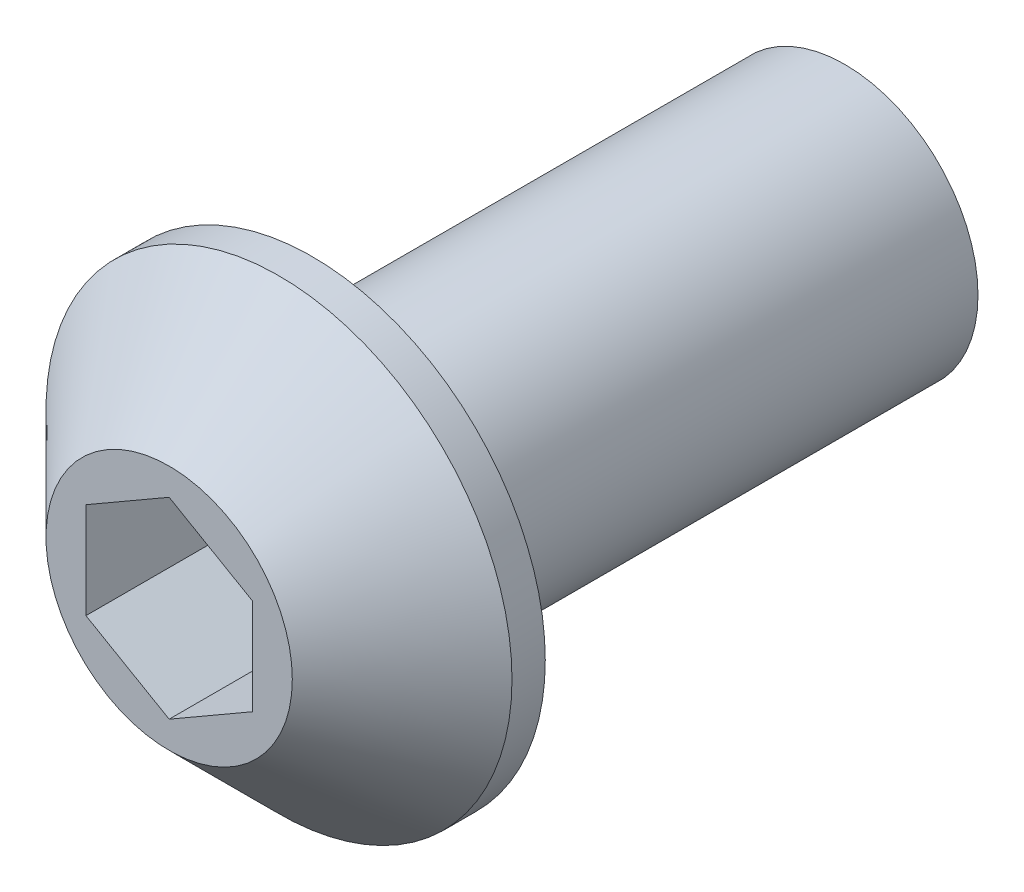
SolidWorks part; units mm, degrees
ref_plane "Plane1" through (0, 0, 0) normal (0, 0, 1) x (1, 0, 0)
ref_plane "Plane2" through (0, 0, 0) normal (0, 1, 0) x (1, 0, 0)
ref_plane "Plane3" through (0, 0, 0) normal (1, 0, 0) x (0, 0, -1)
sketch "Sketch1" plane through (0, 0, 0) normal (0, 0, 1) x (1, 0, 0)
  circle A0 centre (0, 0) radius 7
  dimension "d2 Hoveddiameter" = 14
extrude "Base-Extrude" add sketch "Sketch1" along normal blind 4.3
sketch "Sketch2" plane through (0, 0, 0) normal (0, 0, -1) x (-1, 0, 0)
  circle A0 centre (0, 0) radius 4
  dimension "M Gevind" = 8
extrude "Boss-Extrude1" add sketch "Sketch2" along normal blind 16
sketch "Sketch3" plane through (0, 0, 4.3) normal (0, 0, 1) x (1, 0, 0)
  line L1 (0, 2.8868) -> (-2.5, 1.4434)
  line L2 (-2.5, 1.4434) -> (-2.5, -1.4434)
  line L3 (-2.5, -1.4434) -> (0, -2.8868)
  line L4 (0, -2.8868) -> (2.5, -1.4434)
  line L5 (2.5, -1.4434) -> (2.5, 1.4434)
  line L6 (2.5, 1.4434) -> (0, 2.8868)
  circle A0 centre (0, 0) radius 2.5 construction
  dimension "s Nøglevidde" = 5
extrude "Cut-Extrude1" cut sketch "Sketch3" against normal blind 4.3
chamfer "Chamfer1" distance 3.3 angle 45 1 edges at (7, 0, 4.3)
equation "\"D1@Chamfer1\"=\"k Hovedhøjde@Cut-Extrude1\"-1"
